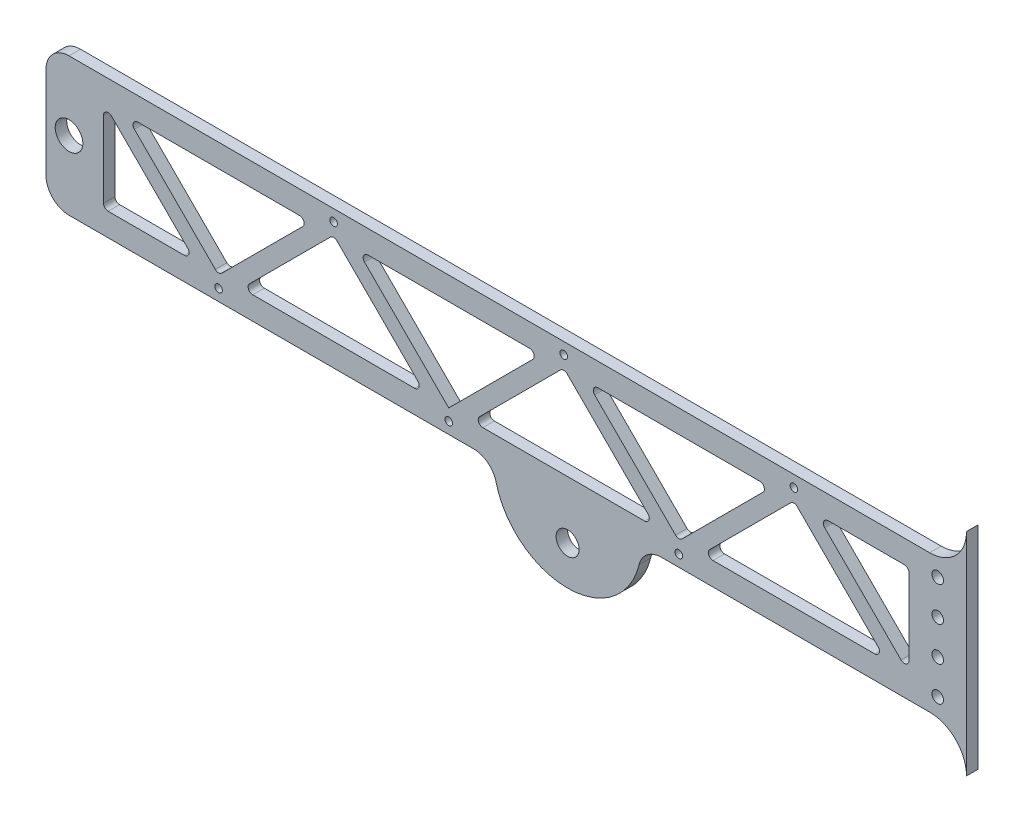
SolidWorks part; units mm, degrees
material "6061 Alloy"
ref_plane "Front Plane" through (0, 0, 0) normal (0, 0, 1) x (1, 0, 0)
ref_plane "Top Plane" through (0, 0, 0) normal (0, 1, 0) x (1, 0, 0)
ref_plane "Right Plane" through (0, 0, 0) normal (1, 0, 0) x (0, 0, -1)
sketch "Sketch1" plane through (0, 0, 0) normal (0, 0, 1) x (1, 0, 0)
  line L1 (-10, 0) -> (-390, 0)
  line L2 (0, 10) -> (0, 50)
  line L3 (-10, 60) -> (-390, 60)
  line L4 (-400, 10) -> (-400, 50)
  arc A0 (-390, 0) -> (-400, 10) centre (-390, 10) cw
  arc A1 (-10, 0) -> (0, 10) centre (-10, 10) ccw
  arc A2 (0, 50) -> (-10, 60) centre (-10, 50) ccw
  arc A3 (-390, 60) -> (-400, 50) centre (-390, 50) ccw
  point P9 (0, 0)
  point P12 (0, 60)
  point P15 (-400, 60)
  dimension "D3" = 10
  dimension "D1" = 400
  dimension "D2" = 60
extrude "Boss-Extrude1" add sketch "Sketch1" along normal blind 5
sketch "Sketch2" plane through (0, 0, 5) normal (0, 0, 1) x (1, 0, 0)
  line L0 (-400, 30) -> (0, 30) construction
  line L5 (-365, 10) -> (-365, 50)
  line L6 (-365, 10) -> (-325, 10)
  line L7 (-400, 50) -> (-400, 10) construction
  line L8 (-325, 10) -> (-325, 50)
  line L9 (-375, 10) -> (-335, 10)
  line L10 (-375, 10) -> (-375, 50)
  line L11 (-375, 50) -> (-335, 50)
  line L12 (-335, 10) -> (-335, 50)
  line L13 (-375, 10) -> (-335, 50) construction
  line L14 (-375, 50) -> (-335, 10) construction
  line L15 (-365, 50) -> (-325, 50)
  line L16 (-355, 10) -> (-355, 50)
  line L17 (-355, 10) -> (-315, 10)
  line L18 (-315, 10) -> (-315, 50)
  line L19 (-355, 50) -> (-315, 50)
  line L20 (-345, 10) -> (-345, 50)
  line L21 (-345, 10) -> (-305, 10)
  line L22 (-305, 10) -> (-305, 50)
  line L23 (-345, 50) -> (-305, 50)
  line L24 (-335, 10) -> (-335, 50)
  line L25 (-335, 10) -> (-295, 10)
  line L26 (-295, 10) -> (-295, 50)
  line L27 (-335, 50) -> (-295, 50)
  line L28 (-325, 10) -> (-325, 50)
  line L29 (-325, 10) -> (-285, 10)
  line L30 (-285, 10) -> (-285, 50)
  line L31 (-325, 50) -> (-285, 50)
  line L32 (-315, 10) -> (-315, 50)
  line L33 (-315, 10) -> (-275, 10)
  line L34 (-275, 10) -> (-275, 50)
  line L35 (-315, 50) -> (-275, 50)
  line L36 (-305, 10) -> (-305, 50)
  line L37 (-305, 10) -> (-265, 10)
  line L38 (-265, 10) -> (-265, 50)
  line L39 (-305, 50) -> (-265, 50)
  line L40 (-295, 10) -> (-295, 50)
  line L41 (-295, 10) -> (-255, 10)
  line L42 (-255, 10) -> (-255, 50)
  line L43 (-295, 50) -> (-255, 50)
  line L44 (-285, 10) -> (-285, 50)
  line L45 (-285, 10) -> (-245, 10)
  line L46 (-245, 10) -> (-245, 50)
  line L47 (-285, 50) -> (-245, 50)
  line L48 (-275, 10) -> (-275, 50)
  line L49 (-275, 10) -> (-235, 10)
  line L50 (-235, 10) -> (-235, 50)
  line L51 (-275, 50) -> (-235, 50)
  line L52 (-265, 10) -> (-265, 50)
  line L53 (-265, 10) -> (-225, 10)
  line L54 (-225, 10) -> (-225, 50)
  line L55 (-265, 50) -> (-225, 50)
  line L56 (-255, 10) -> (-255, 50)
  line L57 (-255, 10) -> (-215, 10)
  line L58 (-215, 10) -> (-215, 50)
  line L59 (-255, 50) -> (-215, 50)
  line L60 (-245, 10) -> (-245, 50)
  line L61 (-245, 10) -> (-205, 10)
  line L62 (-205, 10) -> (-205, 50)
  line L63 (-245, 50) -> (-205, 50)
  line L64 (-235, 10) -> (-235, 50)
  line L65 (-235, 10) -> (-195, 10)
  line L66 (-195, 10) -> (-195, 50)
  line L67 (-235, 50) -> (-195, 50)
  line L68 (-225, 10) -> (-225, 50)
  line L69 (-225, 10) -> (-185, 10)
  line L70 (-185, 10) -> (-185, 50)
  line L71 (-225, 50) -> (-185, 50)
  line L72 (-215, 10) -> (-215, 50)
  line L73 (-215, 10) -> (-175, 10)
  line L74 (-175, 10) -> (-175, 50)
  line L75 (-215, 50) -> (-175, 50)
  line L76 (-205, 10) -> (-205, 50)
  line L77 (-205, 10) -> (-165, 10)
  line L78 (-165, 10) -> (-165, 50)
  line L79 (-205, 50) -> (-165, 50)
  line L80 (-195, 10) -> (-195, 50)
  line L81 (-195, 10) -> (-155, 10)
  line L82 (-155, 10) -> (-155, 50)
  line L83 (-195, 50) -> (-155, 50)
  line L84 (-185, 10) -> (-185, 50)
  line L85 (-185, 10) -> (-145, 10)
  line L86 (-145, 10) -> (-145, 50)
  line L87 (-185, 50) -> (-145, 50)
  line L88 (-175, 10) -> (-175, 50)
  line L89 (-175, 10) -> (-135, 10)
  line L90 (-135, 10) -> (-135, 50)
  line L91 (-175, 50) -> (-135, 50)
  line L92 (-165, 10) -> (-165, 50)
  line L93 (-165, 10) -> (-125, 10)
  line L94 (-125, 10) -> (-125, 50)
  line L95 (-165, 50) -> (-125, 50)
  line L96 (-155, 10) -> (-155, 50)
  line L97 (-155, 10) -> (-115, 10)
  line L98 (-115, 10) -> (-115, 50)
  line L99 (-155, 50) -> (-115, 50)
  line L100 (-145, 10) -> (-145, 50)
  line L101 (-145, 10) -> (-105, 10)
  line L102 (-105, 10) -> (-105, 50)
  line L103 (-145, 50) -> (-105, 50)
  line L104 (-135, 10) -> (-135, 50)
  line L105 (-135, 10) -> (-95, 10)
  line L106 (-95, 10) -> (-95, 50)
  line L107 (-135, 50) -> (-95, 50)
  line L108 (-125, 10) -> (-125, 50)
  line L109 (-125, 10) -> (-85, 10)
  line L110 (-85, 10) -> (-85, 50)
  line L111 (-125, 50) -> (-85, 50)
  line L112 (-115, 10) -> (-115, 50)
  line L113 (-115, 10) -> (-75, 10)
  line L114 (-75, 10) -> (-75, 50)
  line L115 (-115, 50) -> (-75, 50)
  line L116 (-105, 10) -> (-105, 50)
  line L117 (-105, 10) -> (-65, 10)
  line L118 (-65, 10) -> (-65, 50)
  line L119 (-105, 50) -> (-65, 50)
  line L120 (-95, 10) -> (-95, 50)
  line L121 (-95, 10) -> (-55, 10)
  line L122 (-55, 10) -> (-55, 50)
  line L123 (-95, 50) -> (-55, 50)
  line L124 (-85, 10) -> (-85, 50)
  line L125 (-85, 10) -> (-45, 10)
  line L126 (-45, 10) -> (-45, 50)
  line L127 (-85, 50) -> (-45, 50)
  line L128 (-75, 10) -> (-75, 50)
  line L129 (-75, 10) -> (-35, 10)
  line L130 (-35, 10) -> (-35, 50)
  line L131 (-75, 50) -> (-35, 50)
  line L132 (-65, 10) -> (-65, 50)
  line L133 (-65, 10) -> (-25, 10)
  line L134 (-25, 10) -> (-25, 50)
  line L135 (-65, 50) -> (-25, 50)
  line L136 (0, -2.75) -> (0, 2.75) construction
  line L137 (-375, 50) -> (-335, 10)
  line L138 (-365, 50) -> (-325, 10)
  line L139 (-325, 10) -> (-285, 50)
  line L140 (-315, 10) -> (-275, 50)
  line L141 (-275, 50) -> (-235, 10)
  line L142 (-265, 50) -> (-225, 10)
  line L143 (-225, 10) -> (-185, 50)
  line L144 (-215, 10) -> (-175, 50)
  line L145 (-175, 50) -> (-135, 10)
  line L146 (-165, 50) -> (-125, 10)
  line L147 (-125, 10) -> (-85, 50)
  line L148 (-115, 10) -> (-75, 50)
  line L149 (-75, 50) -> (-35, 10)
  line L150 (-65, 50) -> (-25, 10)
  point P3 (-400, 30)
  point P4 (-355, 30)
  dimension "D1" = 25
  dimension "D2" = 40
  dimension "D3" = 40
  dimension "D5" = 25
  dimension "D4" = 32
extrude "Cut-Extrude2" cut sketch "Sketch2" against normal up to next (5 mm away) contours L137 L10 L9 L5 | L137 L5 L6 L16 | L137 L16 L9 L20 | L137 L20 L17 | L140 L21 L22 | L140 L22 L25 L26 | L140 L26 L29 L30 | L140 L30 L33 L34 | L141 L34 L37 L38 | L141 L38 L41 L42 | L141 L42 L45 L46 | L141 L46 L49 | L144 L61 L62 | L144 L62 L65 L66 | L144 L66 L69 L70 | L144 L70 L73 L74 | L145 L74 L77 L78 | L145 L78 L81 L82 | L145 L82 L85 L86 | L145 L86 L89 | L149 L126 L129 | L149 L122 L125 L126 | L149 L118 L121 L122 | L149 L114 L117 L118 | L148 L110 L113 L114 | L148 L106 L109 L110 | L148 L102 L105 L106 | L148 L101 L102 | L130 L150 L134 L135 | L126 L150 L130 L131 | L122 L150 L126 L127 | L123 L150 L122
sketch "Sketch3" plane through (0, 0, 5) normal (0, 0, 1) x (1, 0, 0)
  line L0 (-365, 50) -> (-285, 50)
  line L1 (-285, 50) -> (-325, 10)
  line L2 (-325, 10) -> (-365, 50)
  line L3 (-10, 60) -> (-390, 60) construction
  line L4 (-375, 50) -> (-335, 10) construction
  line L5 (-315, 10) -> (-275, 50) construction
  line L6 (2.75, 0) -> (-2.75, 0) construction
  line L7 (-225, 10) -> (-265, 50)
  line L8 (-265, 50) -> (-185, 50)
  line L9 (-185, 50) -> (-225, 10)
  line L10 (-125, 10) -> (-165, 50)
  line L11 (-165, 50) -> (-85, 50)
  line L12 (-85, 50) -> (-125, 10)
  point P7 (-325, 50)
  dimension "D1" = 80
  dimension "D2" = 10
  dimension "D3" = 10
  dimension "D5" = 100
  dimension "D4" = 3
extrude "Cut-Extrude3" cut sketch "Sketch3" against normal up to next
fillet "Fillet1" radius 2 23 edges at (-65, 50, 2.5) (-215, 10, 2.5) (-275, 50, 2.5) (-265, 50, 2.5) (-175, 50, 2.5) (-165, 50, 2.5) (-75, 50, 2.5) (-115, 10, 2.5) (-125, 10, 2.5) (-185, 50, 2.5) (-85, 50, 2.5) (-25, 50, 2.5) (-25, 10, 2.5) (-35, 10, 2.5) (-135, 10, 2.5) (-235, 10, 2.5) (-315, 10, 2.5) (-365, 50, 2.5) (-285, 50, 2.5) (-325, 10, 2.5) (-335, 10, 2.5) (-375, 50, 2.5) (-375, 10, 2.5)
hole_wizard "M6x1.0 Tapped Hole1" positions "Sketch5" profile "Sketch6" tap size "M6x1.0" standard "ANSI Metric" end condition through all
sketch "Sketch5" plane through (0, 0, 5) normal (0, 0, 1) x (1, 0, 0)
  line L0 (0, -2.75) -> (0, 2.75) construction
  line L1 (-10, 60) -> (-390, 60) construction
  point P0 (-12.5, 52.5)
  point P2 (-12.5, 37.5)
  point P4 (-12.5, 22.5)
  point P6 (-12.5, 7.5)
  dimension "D1" = 12.5
  dimension "D2" = 7.5
  dimension "D3" = 15
  dimension "D4" = 15
  dimension "D5" = 15
sketch "Sketch6" plane through (-12.5, 52.5, 5) normal (1, 0, 0) x (0, -1, 0)
  line L0 (0, 0) -> (0, 5)
  line L1 (0, 5) -> (2.5, 5)
  line L2 (2.5, 5) -> (2.5, 0)
  line L5 (2.5, 0) -> (0, 0)
  line L11 (0, -6.35) -> (0, 107.95) construction
  dimension "Thru Tap Drill Dia." = 5
  dimension "Thru Tap Drill Depth" = 5
cosmetic thread "Hole Thread1" parameters "D2"=6
cosmetic thread "Hole Thread2" parameters "D2"=6
cosmetic thread "Hole Thread3" parameters "D2"=6
cosmetic thread "Hole Thread4" parameters "D2"=6
hole_wizard "M4x0.7 Tapped Hole1" positions "Sketch7" profile "Sketch8" tap size "M4x0.7" standard "ANSI Metric" end condition through all
sketch "Sketch7" plane through (0, 0, 5) normal (0, 0, 1) x (1, 0, 0)
  line L1 (2.75, 0) -> (-2.75, 0) construction
  line L2 (-25, 14.8284) -> (-25, 48) construction
  line L3 (-10, 60) -> (-390, 60) construction
  point P2 (-225, 5)
  point P4 (-175, 55)
  point P6 (-125, 5)
  point P8 (-75, 55)
  point P30 (-275, 55)
  point P33 (-325, 5)
  dimension "D1" = 5
  dimension "D2" = 5
  dimension "D3" = 50
  dimension "D4" = 100
  dimension "D5" = 100
  dimension "D6" = 100
  dimension "D7" = 100
  dimension "D8" = 100
sketch "Sketch8" plane through (-225, 5, 5) normal (1, 0, 0) x (0, -1, 0)
  line L0 (0, 0) -> (0, 5)
  line L1 (0, 5) -> (1.65, 5)
  line L2 (1.65, 5) -> (1.65, 0)
  line L5 (1.65, 0) -> (0, 0)
  line L11 (0, -6.35) -> (0, 107.95) construction
  dimension "Thru Tap Drill Dia." = 3.3
  dimension "Thru Tap Drill Depth" = 5
cosmetic thread "Hole Thread5" parameters "D2"=4
cosmetic thread "Hole Thread6" parameters "D2"=4
cosmetic thread "Hole Thread7" parameters "D2"=4
cosmetic thread "Hole Thread8" parameters "D2"=4
cosmetic thread "Hole Thread9" parameters "D2"=4
cosmetic thread "Hole Thread10" parameters "D2"=4
sketch "Sketch9" plane through (0, 0, 5) normal (0, 0, 1) x (1, 0, 0)
  line L0 (2.75, 0) -> (-2.75, 0) construction
  line L2 (-205.3426, 0) -> (-141.3426, 0)
  arc A0 (-205.3426, 0) -> (-141.3426, 0) centre (-173.3426, 0) ccw
  point P3 (-173.3426, 0)
  dimension "D1" = 32
extrude "Boss-Extrude2" add sketch "Sketch9" against normal up to surface (5 mm away) up to face at (-223.35, 5, 0)
fillet "Fillet2" radius 10 2 edges at (-205.3426, 0, 2.5) (-141.3426, 0, 2.5)
hole_wizard "Ø10.0mm Dowel Hole1" positions "Sketch10" profile "Sketch11" hole size "Ø10.0" standard "ANSI Metric" end condition through all
sketch "Sketch10" plane through (0, 0, 5) normal (0, 0, 1) x (1, 0, 0)
  line L1 (2.75, 0) -> (-2.75, 0) construction
  point P0 (-173.3426, -15)
  point P9 (-325, -15)
  point P10 (-173.3426, -15)
  dimension "D1" = 15
sketch "Sketch11" plane through (-173.3426, -15, 5) normal (1, 0, 0) x (0, -1, 0)
  line L0 (0, 0) -> (0, 5)
  line L1 (0, 5) -> (5, 5)
  line L2 (5, 5) -> (5, 0)
  line L5 (5, 0) -> (0, 0)
  line L11 (0, -6.35) -> (0, 107.95) construction
  dimension "Thru Hole Dia." = 10
  dimension "Thru Hole Depth" = 5
sketch "Sketch12" plane through (0, 0, 5) normal (0, 0, 1) x (1, 0, 0)
  line L0 (0, 76) -> (0, 50)
  line L1 (-10, 60) -> (-390, 60) construction
  line L2 (-132.5505, 0) -> (-10, 0) construction
  line L3 (0, 10) -> (0, -16)
  arc A0 (0, 76) -> (-16, 60) centre (-16, 76) cw
  arc A1 (-16, 60) -> (0, 50) centre (-16, 42.2) cw
  arc A2 (0, -16) -> (-16, 0) centre (-16, -16) ccw
  arc A3 (-16, 0) -> (0, 10) centre (-16, 17.8) ccw
  dimension "D3" = 16
  dimension "D4" = 16
  dimension "D1" = 16
  dimension "D2" = 16
extrude "Boss-Extrude3" add sketch "Sketch12" against normal up to surface (5 mm away) up to face at (-362.0957, 22.9043, 0)
hole_wizard "Ø12.0mm Dowel Hole1" positions "Sketch13" profile "Sketch14" hole size "Ø12.0" standard "ANSI Metric" end condition up to next
sketch "Sketch13" plane through (0, 0, 5) normal (0, 0, 1) x (1, 0, 0)
  line L0 (-390, 60) -> (-390, 0) construction
  point P0 (-390, 30)
  point P8 (-390, 30)
sketch "Sketch14" plane through (-390, 30, 5) normal (1, 0, 0) x (0, -1, 0)
  line L0 (0, 0) -> (0, 5)
  line L1 (0, 5) -> (6, 5)
  line L2 (6, 5) -> (6, 0)
  line L5 (6, 0) -> (0, 0)
  line L11 (0, -6.35) -> (0, 107.95) construction
  dimension "Thru Hole Dia." = 12
  dimension "Thru Hole Depth" = 5
